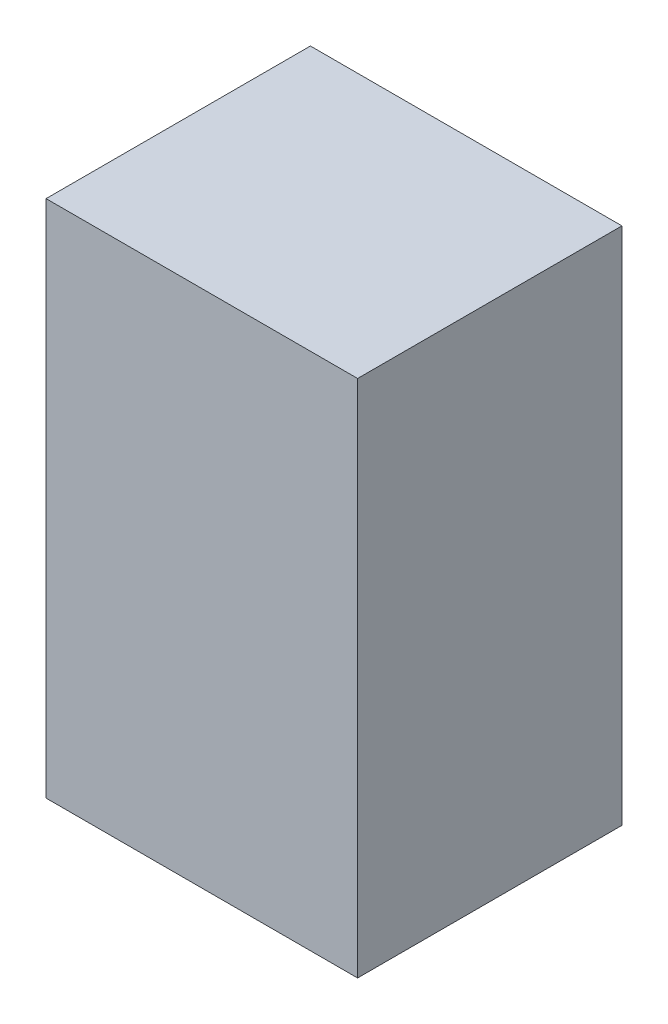
SolidWorks part; units mm, degrees
ref_plane "Front Plane" through (0, 0, 0) normal (0, 0, 1) x (1, 0, 0)
ref_plane "Top Plane" through (0, 0, 0) normal (0, 1, 0) x (1, 0, 0)
ref_plane "Right Plane" through (0, 0, 0) normal (1, 0, 0) x (0, 0, -1)
sketch "Sketch1" plane through (0, 0, 0) normal (0, 1, 0) x (1, 0, 0)
  line L0 (-419.1, 355.6) -> (419.1, -355.6) construction
  line L1 (-419.1, 355.6) -> (419.1, 355.6)
  line L2 (-419.1, 355.6) -> (-419.1, -355.6)
  line L3 (-419.1, -355.6) -> (419.1, -355.6)
  line L4 (419.1, 355.6) -> (419.1, -355.6)
  dimension "D1" = 838.2
  dimension "D2" = 711.2
extrude "Boss-Extrude1" add sketch "Sketch1" along normal blind 1397
sketch "Sketch2" plane through (419.1, 0, 0) normal (1, 0, 0) x (0, 0, -1)
  line L0 (0, 1397) -> (0, 0)
  line L1 (-355.6, 1397) -> (355.6, 1397) construction
